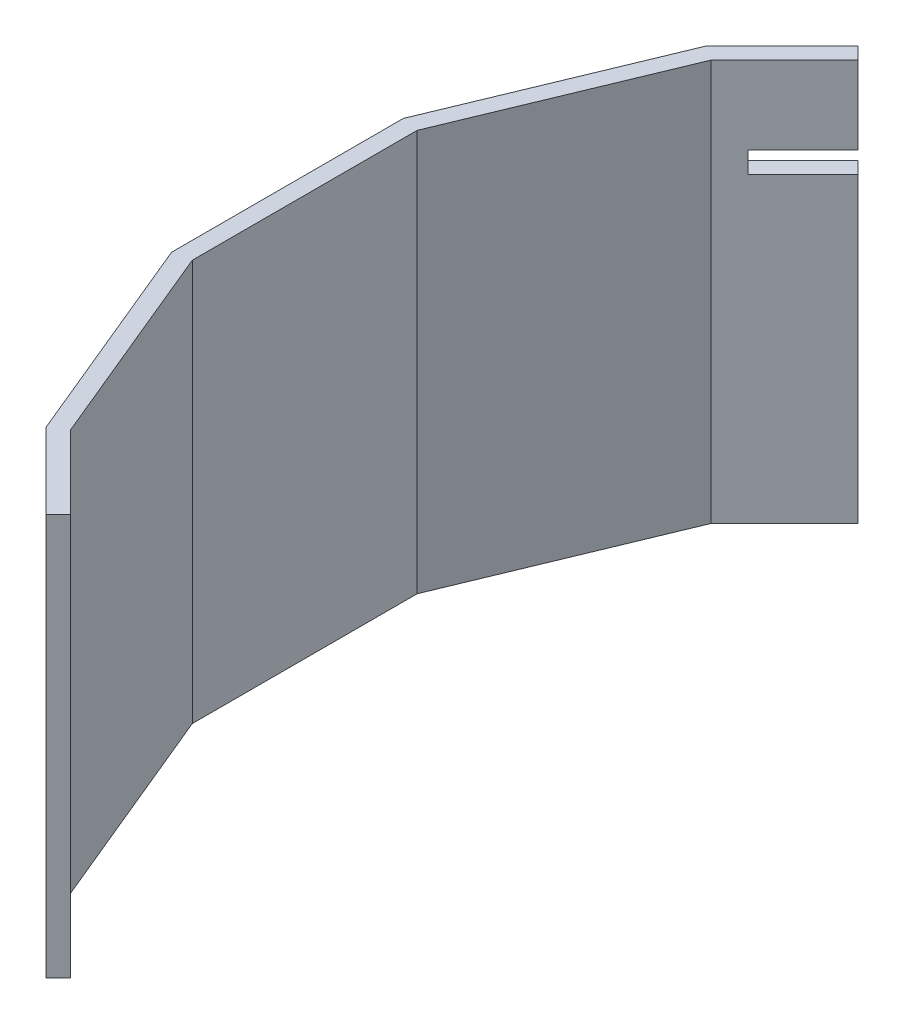
SolidWorks part; units mm, degrees
material "Acrylic (Medium-high impact)"
ref_plane "Front Plane" through (0, 0, 0) normal (0, 0, 1) x (1, 0, 0)
ref_plane "Top Plane" through (0, 0, 0) normal (0, 1, 0) x (1, 0, 0)
ref_plane "Right Plane" through (0, 0, 0) normal (1, 0, 0) x (0, 0, -1)
sketch "Sketch2" plane through (0, 0, 0) normal (0, 1, 0) x (1, 0, 0)
  line L0 (0, 0) -> (-655, 0) construction
  line L1 (0, 0) -> (-605.1411, 250.6576) construction
  line L2 (0, 0) -> (-463.1549, 463.1549) construction
  line L3 (0, 0) -> (-605.1411, -250.6576) construction
  line L4 (0, 0) -> (-463.1549, -463.1549) construction
  line L5 (-555.2822, -371.0277) -> (-371.0277, -555.2822)
  line L6 (-655, 130.2876) -> (-655, -130.2876)
  line L7 (-655, -130.2876) -> (-555.2822, -371.0277)
  line L8 (-555.2822, 371.0277) -> (-655, 130.2876)
  line L9 (-660.5957, 265.7142) -> (-655, 271.3099)
  line L10 (-555.2822, 371.0277) -> (-265.7142, 660.5957)
  line L11 (-572.2374, -382.3568) -> (-385.1698, -569.4243)
  line L12 (-675, -134.2658) -> (-572.2374, -382.3568)
  line L13 (-675, 134.2658) -> (-675, -134.2658)
  line L14 (-572.2374, 382.3568) -> (-675, 134.2658)
  line L15 (-572.2374, 382.3568) -> (-279.8564, 674.7378)
  line L16 (-463.1549, 463.1549) -> (-477.2971, 477.2971)
  line L17 (-463.1549, -463.1549) -> (-477.2971, -477.2971)
  line L18 (-470.226, -456.0839) -> (-484.3681, -470.226)
  line L19 (-484.3681, 470.226) -> (-470.226, 456.0839)
  point P10 (-463.1549, -463.1549)
  point P14 (-655, 0)
  point P17 (-605.1411, -250.6576)
  point P20 (-605.1411, 250.6576)
  point P23 (-463.1549, 463.1549)
  dimension "D1" = 20
  dimension "D2" = 22.5
  dimension "D3" = 22.5
  dimension "D4" = 22.5
  dimension "D5" = 22.5
  dimension "D6" = 10
  dimension "D7" = 10
extrude "Boss-Extrude1" add sketch "Sketch2" along normal blind 465
sketch "Sketch3" plane through (-463.1549, 0, -463.1549) normal (0.7071, 0, 0.7071) x (0.7071, 0, -0.7071)
  line L1 (80, 375) -> (-100, 375)
  line L2 (80, 375) -> (80, 350)
  line L3 (80, 350) -> (-100, 350)
  line L4 (-100, 375) -> (-100, 350)
  line L5 (80, 375) -> (-100, 350) construction
  line L6 (80, 350) -> (-100, 375) construction
  line L7 (-130.2876, 465) -> (-10, 465) construction
  line L8 (-10, 465) -> (-10, 0) construction
  point P0 (-10, 362.5)
  dimension "D1" = 90
  dimension "D2" = 115
  dimension "D3" = 180
extrude "Cut-Extrude1" cut sketch "Sketch3" against normal blind 40 contours L3 L4 L1 L2
